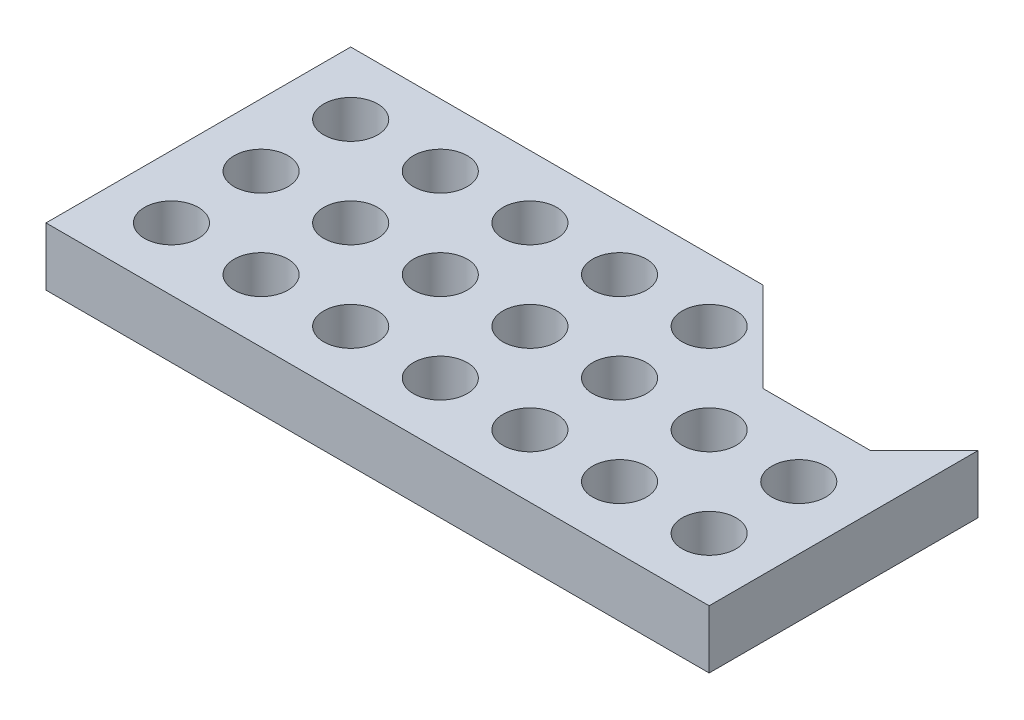
SolidWorks part; units mm, degrees
material "ABS"
ref_plane "Front Plane" through (0, 0, 0) normal (0, 0, 1) x (1, 0, 0)
ref_plane "Top Plane" through (0, 0, 0) normal (0, 1, 0) x (1, 0, 0)
ref_plane "Right Plane" through (0, 0, 0) normal (1, 0, 0) x (0, 0, -1)
sketch "Sketch1" plane through (0, 0, 0) normal (0, 1, 0) x (1, 0, 0)
  line L0 (-18.5, 8.5) -> (18.5, -8.5) construction
  line L1 (-18.5, 8.5) -> (4.5, 8.5)
  line L2 (-18.5, 8.5) -> (-18.5, -8.5)
  line L3 (-18.5, -8.5) -> (18.5, -8.5)
  line L4 (18.5, 6.5) -> (18.5, -8.5)
  line L5 (4.5, 8.5) -> (9.5, 3.5)
  line L6 (9.5, 3.5) -> (15.5, 3.5)
  line L7 (15.5, 3.5) -> (18.5, 6.5)
  circle A0 centre (-15, -5) radius 1.5025
  circle A1 centre (-10, -5) radius 1.5025
  circle A2 centre (-5, -5) radius 1.5025
  circle A3 centre (0, -5) radius 1.5025
  circle A4 centre (5, -5) radius 1.5025
  circle A5 centre (10, -5) radius 1.5025
  circle A6 centre (15, -5) radius 1.5025
  circle A7 centre (-10, 0) radius 1.5025
  circle A8 centre (-5, 0) radius 1.5025
  circle A9 centre (0, 0) radius 1.5025
  circle A10 centre (5, 0) radius 1.5025
  circle A11 centre (10, 0) radius 1.5025
  circle A12 centre (15, 0) radius 1.5025
  circle A13 centre (-10, 5) radius 1.5025
  circle A14 centre (-5, 5) radius 1.5025
  circle A15 centre (0, 5) radius 1.5025
  circle A16 centre (5, 5) radius 1.5025
  circle A19 centre (-15, 0) radius 1.5025
  circle A20 centre (-15, 5) radius 1.5025
  arc A21 (9.3525, 3.6442) -> (10, 3.4975) centre (10, 5) ccw [skipped]
  arc A22 (15, 3.4975) -> (15.6475, 3.6442) centre (15, 5) ccw [skipped]
  dimension "D7" = 3.5
  dimension "D8" = 3.5
  dimension "D9" = 3.005
  dimension "D12" = 3.5
  dimension "D13" = 3.5
  dimension "D14" = 3.5
  dimension "D15" = 3.5
  dimension "D2" = 17
  dimension "D3" = 6
  dimension "D4" = 14
  dimension "D5" = 15
  dimension "D6" = 12
  dimension "D16" = 5
  dimension "D17" = 37
  dimension "D10" = 7
  dimension "D11" = 3
extrude "Boss-Extrude1" add sketch "Sketch1" along normal blind 3.25
